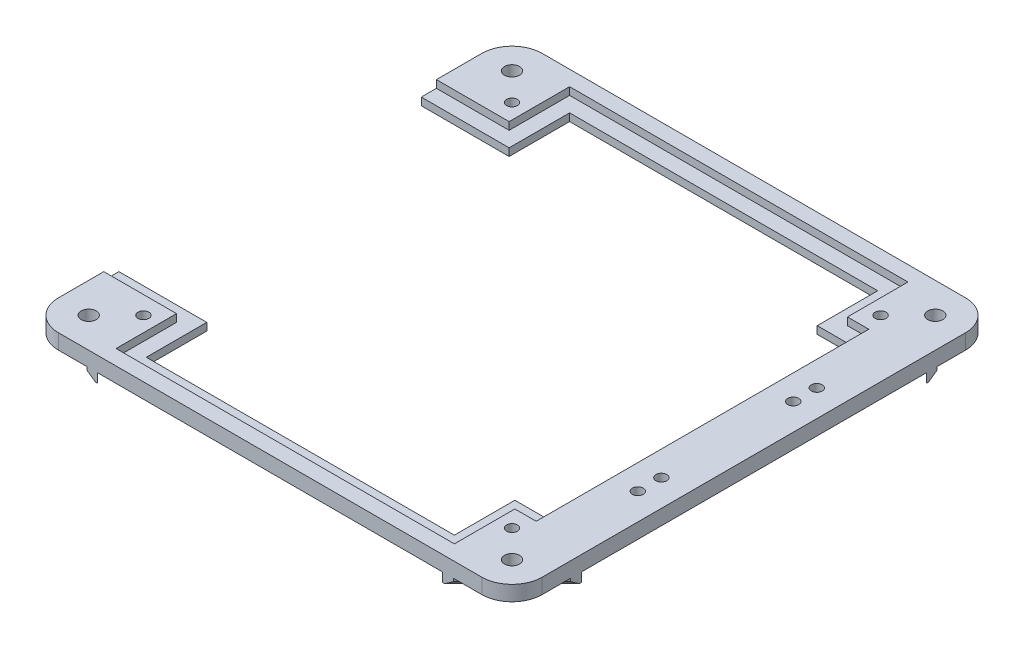
SolidWorks part; units mm, degrees
ref_plane "Front Plane" through (0, 0, 0) normal (0, 0, 1) x (1, 0, 0)
ref_plane "Top Plane" through (0, 0, 0) normal (0, 1, 0) x (1, 0, 0)
ref_plane "Right Plane" through (0, 0, 0) normal (1, 0, 0) x (0, 0, -1)
sketch "Sketch1" plane through (0, 0, 0) normal (0, 1, 0) x (1, 0, 0)
  line L0 (0, 0) -> (0, 25.4)
  line L1 (12.7, 38.1) -> (190.5, 38.1)
  line L2 (203.2, 25.4) -> (203.2, -152.4)
  line L3 (190.5, -165.1) -> (12.7, -165.1)
  line L4 (0, -152.4) -> (0, -127)
  line L5 (0, -127) -> (181.61, -127)
  line L6 (181.61, -127) -> (181.61, 0)
  line L7 (181.61, 0) -> (0, 0)
  arc A0 (12.7, -165.1) -> (0, -152.4) centre (12.7, -152.4) cw
  arc A1 (203.2, -152.4) -> (190.5, -165.1) centre (190.5, -152.4) cw
  arc A2 (190.5, 38.1) -> (203.2, 25.4) centre (190.5, 25.4) cw
  arc A3 (0, 25.4) -> (12.7, 38.1) centre (12.7, 25.4) cw
  point P13 (203.2, -165.1)
  point P16 (203.2, 38.1)
  point P19 (0, 38.1)
  dimension "D6" = 12.7
  dimension "D1" = 203.2
  dimension "D2" = 38.1
  dimension "D3" = 203.2
  dimension "D4" = 181.61
  dimension "D5" = 127
extrude "Boss-Extrude2" add sketch "Sketch1" along normal blind 6.35
sketch "Sketch2" plane through (0, 6.35, 0) normal (0, 1, 0) x (1, 0, 0)
  circle A0 centre (12.7, 25.4) radius 3.175
  circle A1 centre (190.5, 25.4) radius 3.175
  circle A2 centre (190.5, -152.4) radius 3.175
  circle A3 centre (12.7, -152.4) radius 3.175
  arc A4 (12.7, 38.1) -> (0, 25.4) centre (12.7, 25.4) ccw construction
  dimension "D1" = 6.35
extrude "Cut-Extrude1" cut sketch "Sketch2" against normal through all
sketch "Sketch7" plane through (0, 6.35, 0) normal (0, 1, 0) x (1, 0, 0)
  line L0 (192.024, -28.194) -> (192.024, -33.528) construction
  line L1 (192.024, -38.1) -> (192.024, -88.9) construction
  line L2 (192.024, -93.472) -> (192.024, -98.806) construction
  line L3 (192.024, -23.622) -> (192.024, 38.1) construction
  line L4 (190.5, 38.1) -> (12.7, 38.1) construction
  line L5 (192.024, -103.378) -> (192.024, -165.1) construction
  line L6 (12.7, -165.1) -> (190.5, -165.1) construction
  line L7 (189.738, -25.908) -> (181.61, -25.908) construction
  line L8 (181.61, 0) -> (181.61, -127) construction
  circle A0 centre (192.024, -101.092) radius 2.286
  circle A1 centre (192.024, -91.186) radius 2.286
  circle A2 centre (192.024, -35.814) radius 2.286
  circle A3 centre (192.024, -25.908) radius 2.286
  dimension "D1" = 4.572
  dimension "D2" = 5.334
  dimension "D3" = 5.334
  dimension "D4" = 50.8
  dimension "D5" = 8.128
extrude "Cut-Extrude3" cut sketch "Sketch7" against normal blind 12.7
sketch "Sketch8" plane through (0, 0, 0) normal (0, -1, 0) x (-1, 0, 0)
  line L0 (-3.7197, -161.3803) -> (-199.4803, 34.3803) construction
  line L1 (-24.1978, 13.9022) -> (-24.1978, 38.1) construction
  line L2 (-190.5, 38.1) -> (-12.7, 38.1) construction
  line L3 (-24.1978, 13.9022) -> (0, 13.9022) construction
  line L5 (-24.1978, 13.9022) -> (-3.7197, 34.3803) construction
  line L6 (0, 25.4) -> (0, 0) construction
  arc A0 (0, 25.4) -> (-12.7, 38.1) centre (-12.7, 25.4) ccw construction
  circle A1 centre (-24.1978, 13.9022) radius 2.286
  arc A2 (-12.7, -165.1) -> (0, -152.4) centre (-12.7, -152.4) ccw construction
  arc A3 (-190.5, 38.1) -> (-203.2, 25.4) centre (-190.5, 25.4) ccw construction
  circle A4 centre (-24.1978, -140.9022) radius 2.286
  circle A5 centre (-179.0022, -140.9022) radius 2.286
  circle A6 centre (-179.0022, 13.9022) radius 2.286
  point P8 (-101.6, -63.5)
  dimension "D2" = 4.572
  dimension "D1" = 28.9603
  dimension "D3" = 4
extrude "Cut-Extrude4" cut sketch "Sketch8" against normal through all
sketch "Sketch9" plane through (0, 6.35, 0) normal (0, 1, 0) x (1, 0, 0)
  line L0 (0, 0) -> (181.61, 0) construction
  line L1 (36.8978, 0) -> (166.3022, 0)
  line L2 (36.8978, 0) -> (36.8978, 25.4)
  line L3 (36.8978, 25.4) -> (166.3022, 25.4)
  line L4 (166.3022, 0) -> (166.3022, 25.4)
  line L5 (181.61, -127) -> (0, -127) construction
  line L6 (166.3022, -127) -> (36.8978, -127)
  line L7 (166.3022, -127) -> (166.3022, -152.4)
  line L8 (166.3022, -152.4) -> (36.8978, -152.4)
  line L9 (36.8978, -127) -> (36.8978, -152.4)
  line L10 (12.7, -165.1) -> (190.5, -165.1) construction
  line L11 (190.5, 38.1) -> (12.7, 38.1) construction
  circle A0 centre (179.0022, 13.9022) radius 2.286 construction
  circle A1 centre (24.1978, 13.9022) radius 2.286 construction
  point P12 (101.6, -152.4)
  point P15 (101.6, -165.1)
  dimension "D1" = 12.7
  dimension "D2" = 12.7
  dimension "D3" = 12.7
extrude "Cut-Extrude5" cut sketch "Sketch9" against normal through all
sketch "Sketch10" plane through (0, 6.35, 0) normal (0, 1, 0) x (1, 0, 0)
  line L0 (0, 6.35) -> (30.5478, 6.35)
  line L1 (0, 25.4) -> (0, 0) construction
  line L2 (30.5478, 6.35) -> (30.5478, 31.75)
  line L3 (30.5478, 31.75) -> (172.6522, 31.75)
  line L4 (172.6522, 31.75) -> (172.6522, 6.35)
  line L5 (172.6522, 6.35) -> (181.61, 6.35)
  line L6 (181.61, 6.35) -> (181.61, 0)
  line L7 (166.3022, 0) -> (181.61, 0) construction
  line L8 (181.61, 0) -> (181.61, -127) construction
  line L9 (181.61, 0) -> (166.3022, 0)
  line L10 (166.3022, 0) -> (166.3022, 25.4)
  line L11 (166.3022, 25.4) -> (36.8978, 25.4)
  line L12 (36.8978, 25.4) -> (36.8978, 0)
  line L13 (36.8978, 0) -> (0, 0)
  line L14 (0, 0) -> (0, 6.35)
  line L15 (-796.8, -63.5) -> (49203.2, -63.5) construction
  line L16 (203.2, -152.4) -> (203.2, 25.4) construction
  line L17 (0, -127) -> (0, -133.35)
  line L18 (36.8978, -127) -> (0, -127)
  line L19 (36.8978, -152.4) -> (36.8978, -127)
  line L20 (166.3022, -152.4) -> (36.8978, -152.4)
  line L21 (166.3022, -127) -> (166.3022, -152.4)
  line L22 (181.61, -127) -> (166.3022, -127)
  line L23 (181.61, -133.35) -> (181.61, -127)
  line L24 (172.6522, -133.35) -> (181.61, -133.35)
  line L25 (172.6522, -158.75) -> (172.6522, -133.35)
  line L26 (30.5478, -158.75) -> (172.6522, -158.75)
  line L27 (30.5478, -133.35) -> (30.5478, -158.75)
  line L28 (0, -133.35) -> (30.5478, -133.35)
  point P28 (203.2, -63.5)
  dimension "D1" = 6.35
  dimension "D2" = 6.35
  dimension "D3" = 6.35
  dimension "D4" = 6.35
  dimension "D5" = 6.35
extrude "Cut-Extrude6" cut sketch "Sketch10" against normal blind 3.175
sketch "Sketch11" plane through (0, 0, 0) normal (0, -1, 0) x (1, 0, 0)
  line L0 (174.0713, -38.1) -> (187.3849, -24.7864)
  line L1 (190.5, -38.1) -> (12.7, -38.1) construction
  line L2 (203.2, 152.4) -> (203.2, -25.4) construction
  line L3 (203.2, -8.9713) -> (203.2, -13.4614)
  line L4 (203.2, -13.4614) -> (193.0933, -23.5682)
  line L5 (178.5614, -38.1) -> (174.0713, -38.1)
  line L6 (189.8864, -22.2849) -> (203.2, -8.9713)
  line L7 (188.6682, -27.9933) -> (178.5614, -38.1)
  line L8 (3.7197, -34.3803) -> (199.4803, 161.3803) construction
  line L9 (10.1067, -23.5682) -> (0, -13.4614)
  line L10 (0, -13.4614) -> (0, -8.9713)
  line L11 (0, -8.9713) -> (13.3136, -22.2849)
  line L12 (15.8151, -24.7864) -> (29.1287, -38.1)
  line L13 (24.6386, -38.1) -> (14.5318, -27.9933)
  line L14 (29.1287, -38.1) -> (24.6386, -38.1)
  line L15 (14.5318, 154.9933) -> (24.6386, 165.1)
  line L16 (24.6386, 165.1) -> (29.1287, 165.1)
  line L17 (29.1287, 165.1) -> (15.8151, 151.7864)
  line L18 (13.3136, 149.2849) -> (0, 135.9713)
  line L19 (0, 140.4614) -> (10.1067, 150.5682)
  line L20 (0, 135.9713) -> (0, 140.4614)
  line L21 (193.0933, 150.5682) -> (203.2, 140.4614)
  line L22 (203.2, 140.4614) -> (203.2, 135.9713)
  line L23 (203.2, 135.9713) -> (189.8864, 149.2849)
  line L24 (187.3849, 151.7864) -> (174.0713, 165.1)
  line L25 (178.5614, 165.1) -> (188.6682, 154.9933)
  line L26 (174.0713, 165.1) -> (178.5614, 165.1)
  arc A0 (187.3849, -24.7864) -> (188.6682, -27.9933) centre (190.5, -25.4) ccw
  arc A1 (193.0933, -23.5682) -> (189.8864, -22.2849) centre (190.5, -25.4) ccw
  arc A2 (0, -25.4) -> (12.7, -38.1) centre (12.7, -25.4) ccw construction
  arc A3 (203.2, 152.4) -> (190.5, 165.1) centre (190.5, 152.4) ccw construction
  arc A4 (13.3136, -22.2849) -> (10.1067, -23.5682) centre (12.7, -25.4) ccw
  arc A5 (14.5318, -27.9933) -> (15.8151, -24.7864) centre (12.7, -25.4) ccw
  arc A6 (15.8151, 151.7864) -> (14.5318, 154.9933) centre (12.7, 152.4) ccw
  arc A7 (10.1067, 150.5682) -> (13.3136, 149.2849) centre (12.7, 152.4) ccw
  arc A8 (189.8864, 149.2849) -> (193.0933, 150.5682) centre (190.5, 152.4) ccw
  arc A9 (188.6682, 154.9933) -> (187.3849, 151.7864) centre (190.5, 152.4) ccw
  point P22 (101.6, 63.5)
  dimension "D4" = 6.35
  dimension "D1" = 29.1287
  dimension "D2" = 29.1287
  dimension "D3" = 3.175
  dimension "D6" = 177.8
  dimension "D7" = 125.7236
  dimension "D5" = 4
extrude "Boss-Extrude3" add sketch "Sketch11" along normal blind 3.81
chamfer "Chamfer1" distance 2.54 angle 45 8 edges at (198.1466, -3.81, 145.5148) (183.6148, -3.81, 160.0466) (19.5852, -3.81, 160.0466) (5.0534, -3.81, 145.5148) (5.0534, -3.81, -18.5148) (19.5852, -3.81, -33.0466) (198.1466, -3.81, -18.5148) (183.6148, -3.81, -33.0466)
